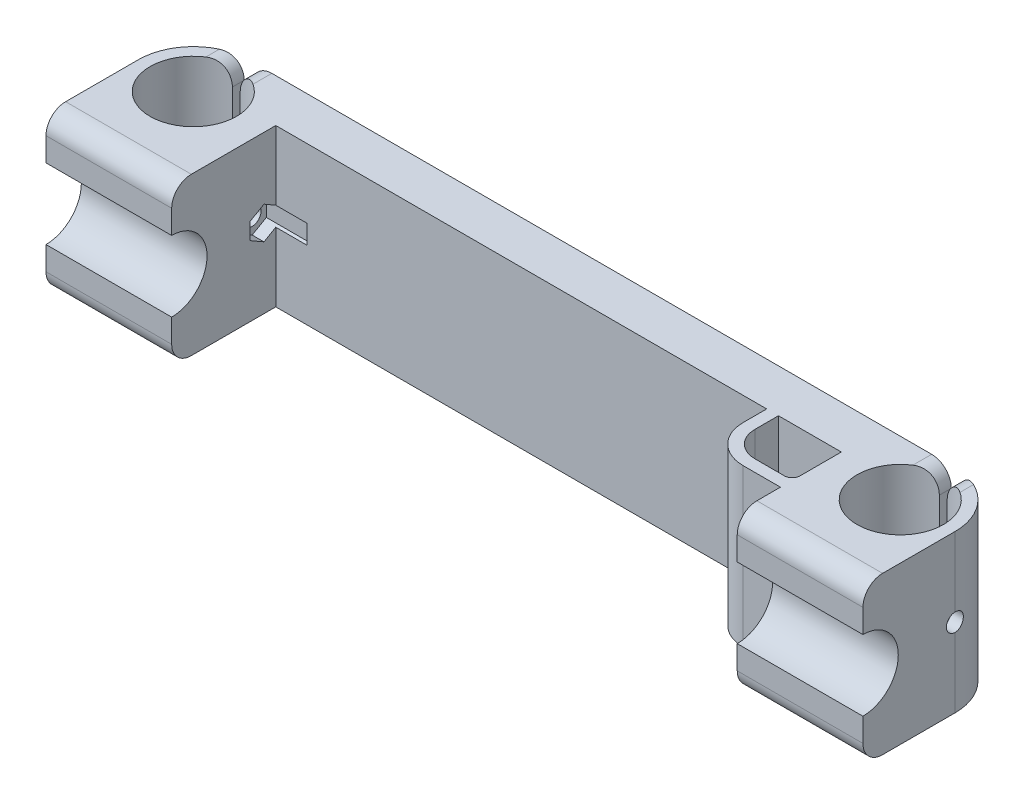
SolidWorks part; units mm, degrees
ref_plane "Front Plane" through (0, 0, 0) normal (0, 0, 1) x (1, 0, 0)
ref_plane "Top Plane" through (0, 0, 0) normal (0, 1, 0) x (1, 0, 0)
ref_plane "Right Plane" through (0, 0, 0) normal (1, 0, 0) x (0, 0, -1)
sketch "Sketch1" plane through (0, 0, 0) normal (0, 1, 0) x (1, 0, 0)
  line L0 (137.4606, -14.5) -> (119.4606, -14.5)
  line L1 (119.4606, -14.5) -> (119.4606, 7.5)
  line L2 (-42.5394, -14.5) -> (-24.5394, -14.5)
  line L3 (-42.5394, 13.5) -> (137.4606, 13.5)
  line L4 (119.4606, 7.5) -> (-24.5394, 7.5)
  line L5 (-24.5394, -14.5) -> (-24.5394, 7.5)
  line L6 (-56.5394, -0.5) -> (-56.5394, -14.5)
  line L7 (-56.5394, -14.5) -> (-42.5394, -14.5)
  line L8 (137.4606, -14.5) -> (151.4606, -14.5)
  line L9 (151.4606, -14.5) -> (151.4606, -0.5)
  circle A0 centre (-42.5394, -0.5) radius 11
  circle A1 centre (137.4606, -0.5) radius 11
  arc A2 (-56.5394, -0.5) -> (-42.5394, 13.5) centre (-42.5394, -0.5) cw
  arc A6 (137.4606, 13.5) -> (151.4606, -0.5) centre (137.4606, -0.5) cw
  dimension "D3" = 22
  dimension "D4" = 22
  dimension "D5" = 180
  dimension "D6" = 3
  dimension "D1" = 18
  dimension "D2" = 18
  dimension "D8" = 6
extrude "Boss-Extrude1" add sketch "Sketch1" along normal blind 40
sketch "Sketch2" plane through (-56.5394, 0, 0) normal (-1, 0, 0) x (0, 0, 1)
  line L0 (14.5, 40) -> (19, 40)
  line L1 (24, 35) -> (24, 29)
  line L2 (24, 11) -> (24, 5)
  line L3 (19, 0) -> (14.5, 0)
  line L4 (14.5, 0) -> (14.5, 40)
  arc A0 (24, 29) -> (24, 11) centre (24, 20) ccw
  arc A1 (24, 5) -> (19, 0) centre (19, 5) cw
  arc A2 (19, 40) -> (24, 35) centre (19, 35) cw
  point P11 (24, 0)
  dimension "D1" = 9
  dimension "D3" = 5
  dimension "D2" = 9.5
extrude "Boss-Extrude2" add sketch "Sketch2" against normal up to surface (32 mm away) up to face at (-24.5394, 20, 3.5)
ref_plane "Plane1" through (47.4606, 0, 0) normal (-1, 0, 0) x (0, 0, 1)
sketch "Sketch3" plane through (151.4606, 0, 0) normal (1, 0, 0) x (0, 0, -1)
  line L0 (-14.5, 0) -> (-14.5, 40)
  line L5 (-19, 0) -> (7.5, 0)
  line L6 (7.5, 0) -> (7.5, 40)
  line L7 (7.5, 40) -> (-19, 40)
  line L8 (-24, 35) -> (-24, 29)
  line L9 (-24, 11) -> (-24, 5)
  line L10 (-19, 0) -> (-14.5, 0)
  line L12 (-14.5, 40) -> (-19, 40)
  line L13 (-24, 35) -> (-24, 29)
  line L14 (-24, 11) -> (-24, 5)
  line L15 (7.5, 0) -> (7.5, 40)
  arc A3 (-19, 40) -> (-24, 35) centre (-19, 35) ccw
  arc A4 (-24, 11) -> (-24, 29) centre (-24, 20) ccw
  arc A5 (-24, 5) -> (-19, 0) centre (-19, 5) ccw
  arc A6 (-19, 40) -> (-24, 35) centre (-19, 35) ccw
  arc A7 (-24, 11) -> (-24, 29) centre (-24, 20) ccw
  arc A8 (-24, 5) -> (-19, 0) centre (-19, 5) ccw
  line M12 (-14.5, 40) -> (-14.5, 0)
  dimension "D1" = 0
sketch "Sketch4" plane through (0, 0, -7.5) normal (0, 0, 1) x (1, 0, 0)
  line L0 (119.4606, 40) -> (119.4606, 0) construction
  line L1 (119.4606, 40) -> (-24.5394, 40)
  line L2 (119.4606, 40) -> (119.4606, 0)
  line L3 (119.4606, 0) -> (-24.5394, 0)
  line L4 (-24.5394, 40) -> (-24.5394, 0)
  line L5 (-24.5394, 40) -> (-24.5394, 0) construction
  line L6 (-24.5394, 0) -> (119.4606, 0) construction
  dimension "D1" = 0
  dimension "D2" = 40
extrude "Boss-Extrude4" add sketch "Sketch4" along normal blind 5
extrude "Boss-Extrude5" add sketch "Sketch3" against normal up to surface (32 mm away) contours L14 A8 L10 L12 A6 L13 A7 M12 up to face at (119.4606, 20, 6)
sketch "Sketch5" plane through (0, 0, -13.5) normal (0, 0, -1) x (-1, 0, 0)
  line L0 (-137.4606, 20) -> (42.5394, 20) construction
  line L1 (-137.4606, 40) -> (-137.4606, 0) construction
  line L2 (42.5394, 40) -> (42.5394, 0) construction
  line L3 (-137.4606, 40) -> (42.5394, 40) construction
  line L4 (32.5394, 35) -> (-127.4606, 35)
  line L5 (37.5394, 30) -> (37.5394, 10)
  line L6 (32.5394, 5) -> (-127.4606, 5)
  line L7 (-132.4606, 30) -> (-132.4606, 10)
  line L8 (37.5394, 35) -> (-132.4606, 5) construction
  line L9 (37.5394, 5) -> (-132.4606, 35) construction
  arc A0 (32.5394, 35) -> (37.5394, 30) centre (32.5394, 30) cw
  arc A1 (37.5394, 10) -> (32.5394, 5) centre (32.5394, 10) cw
  arc A2 (-127.4606, 5) -> (-132.4606, 10) centre (-127.4606, 10) cw
  arc A3 (-127.4606, 35) -> (-132.4606, 30) centre (-127.4606, 30) ccw
  point P6 (-47.4606, 20)
  dimension "D3" = 5
  dimension "D1" = 5
  dimension "D2" = 5
extrude "Cut-Extrude2" cut sketch "Sketch5" against normal blind 3
sketch "Sketch6" plane through (0, 0, -10.5) normal (0, 0, -1) x (-1, 0, 0)
  line L0 (-47.4606, 35) -> (-47.4606, 5) construction
  line L1 (32.5394, 35) -> (-127.4606, 35) construction
  line L2 (-127.4606, 5) -> (32.5394, 5) construction
  line L4 (12.5394, 10) -> (-107.4606, 10)
  line L5 (12.5394, 10) -> (12.5394, 30)
  line L6 (12.5394, 30) -> (-107.4606, 30)
  line L7 (-107.4606, 10) -> (-107.4606, 30)
  line L8 (12.5394, 10) -> (-107.4606, 30) construction
  line L9 (12.5394, 30) -> (-107.4606, 10) construction
  point P6 (-47.4606, 20)
  dimension "D1" = 120
  dimension "D2" = 20
extrude "Cut-Extrude3" cut sketch "Sketch6" against normal blind 5
sketch "Sketch8" plane through (0, 0, -13.5) normal (0, 0, -1) x (-1, 0, 0)
  line L0 (-137.4606, 40) -> (-137.4606, 0)
  line L1 (42.5394, 40) -> (42.5394, 0)
extrude "Cut-Extrude-Thin1" cut sketch "Sketch8" against normal blind 18 thin thin type mid plane wall 2
fillet "Fillet2" radius 5 8 edges at (-43.5394, 40, -11.9593) (-41.5394, 40, -11.9772) (-43.5394, 0, -11.9593) (-41.5394, 0, -11.9772) (136.4606, 0, -11.9772) (138.4606, 0, -11.9593) (138.4606, 40, -11.9593) (136.4606, 40, -11.9772)
sketch "Sketch9" plane through (151.4606, 0, 0) normal (1, 0, 0) x (0, 0, -1)
  line L0 (-0.5, 40) -> (-0.5, 0) construction
  circle A0 centre (-0.5, 20) radius 2.25
  dimension "D1" = 4.5
extrude "Cut-Extrude4" cut sketch "Sketch9" against normal blind 226
sketch "Sketch10" plane through (-24.5394, 0, 0) normal (1, 0, 0) x (0, 0, -1)
  line L1 (-0.5, 24.1569) -> (-4.1, 22.0785)
  line L2 (-4.1, 22.0785) -> (-4.1, 17.9215)
  line L3 (-4.1, 17.9215) -> (-0.5, 15.8431)
  line L4 (-0.5, 15.8431) -> (3.1, 17.9215)
  line L5 (3.1, 17.9215) -> (3.1, 22.0785)
  line L6 (3.1, 22.0785) -> (-0.5, 24.1569)
  circle A0 centre (-0.5, 20) radius 3.6 construction
  dimension "D1" = 7.2
extrude "Cut-Extrude5" cut sketch "Sketch10" against normal blind 3 and the other way blind 8
mirror "Mirror5" about plane through (47.4606, 0, 0) normal (-1, 0, 0) of "Cut-Extrude5"
sketch "Sketch12" plane through (0, 0, 0) normal (0, -1, 0) x (-1, 0, 0)
  line L0 (-109.9606, -0.5) -> (-109.9606, -3.5) construction
  line L1 (24.5394, 2.5) -> (-119.4606, 2.5) construction
  line L2 (-103.4606, -3.5) -> (-103.4606, 2.5)
  line L4 (-116.4606, -10) -> (-119.4606, -10)
  line L5 (-100.4606, -3.5) -> (-100.4606, 2.5)
  line L8 (-119.4606, 2.5) -> (-119.4606, -19) construction
  line L9 (-109.9606, -13) -> (-119.4606, -13)
  line L10 (-119.4606, -13) -> (-119.4606, -10)
  line L11 (-109.9606, -10) -> (-116.4606, -10)
  line L13 (-103.4606, 2.5) -> (-100.4606, 2.5)
  line L14 (-116.4606, 2.5) -> (-116.4606, -3.5) construction
  line L15 (-119.4606, 5.5) -> (-119.4606, -3.5) construction
  line L16 (-100.4606, 5.5) -> (-119.4606, 5.5) construction
  line L17 (-100.4606, -3.5) -> (-100.4606, 5.5) construction
  line L18 (-103.4606, 2.5) -> (-116.4606, 2.5) construction
  arc A0 (-109.9606, -10) -> (-103.4606, -3.5) centre (-109.9606, -3.5) ccw
  arc A1 (-109.9606, -13) -> (-100.4606, -3.5) centre (-109.9606, -3.5) ccw
  arc A3 (-119.4606, -3.5) -> (-100.4606, -3.5) centre (-109.9606, -3.5) ccw construction
  arc A4 (-116.4606, -3.5) -> (-103.4606, -3.5) centre (-109.9606, -3.5) ccw construction
  dimension "D1" = 13
  dimension "D4" = 6
  dimension "D2" = 3
  dimension "D3" = 3
extrude "Boss-Extrude6" add sketch "Sketch12" against normal up to surface (40 mm away) up to face at (47.4606, 40, 1.4966)
fillet "Fillet3" radius 2 1 edges at (119.4606, 20, 10)
